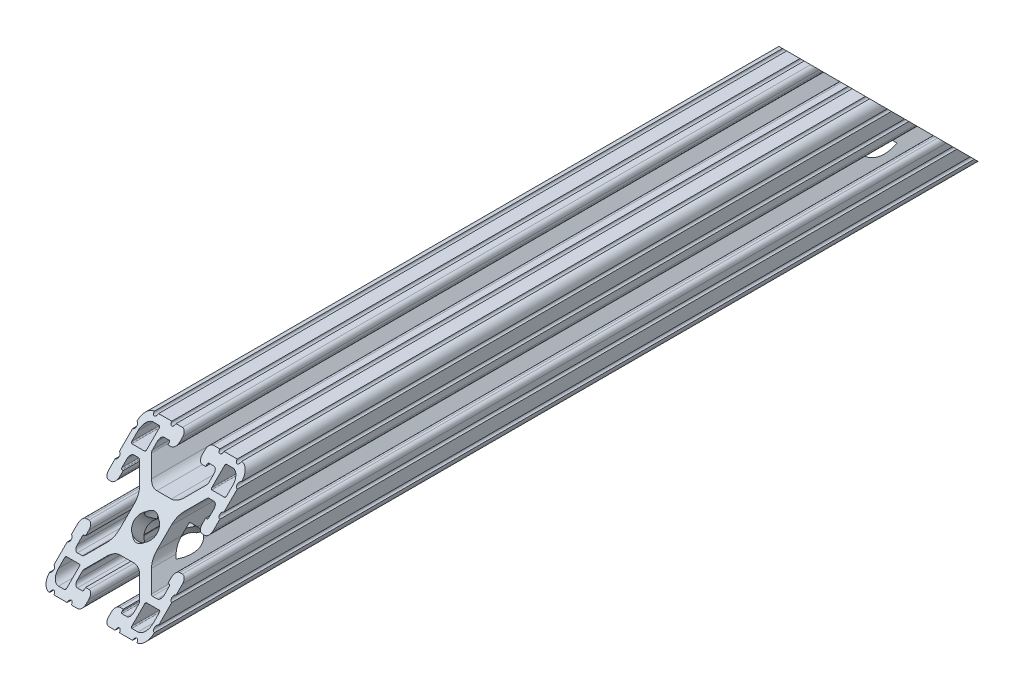
SolidWorks part; units mm, degrees
material "6105-T5 Aluminum"
ref_plane "Front Plane" through (0, 0, 0) normal (0, 0, 1) x (1, 0, 0)
ref_plane "Top Plane" through (0, 0, 0) normal (0, 1, 0) x (1, 0, 0)
ref_plane "Right Plane" through (0, 0, 0) normal (1, 0, 0) x (0, 0, -1)
sketch "Sketch1" plane through (0, 0, 0) normal (0, 0, 1) x (1, 0, 0)
  line L0 (16.8656, 11.8618) -> (12.2428, 11.8618)
  line L1 (11.8618, 12.2428) -> (11.8618, 16.8656)
  line L2 (12.2428, 17.2466) -> (14.4526, 17.2466)
  line L3 (17.2466, 14.4526) -> (17.2466, 12.2428)
  line L4 (-16.8656, -11.8618) -> (-12.2428, -11.8618)
  line L5 (-11.8618, -12.2428) -> (-11.8618, -16.8656)
  line L6 (-12.2428, -17.2466) -> (-14.4526, -17.2466)
  line L7 (-17.2466, -14.4526) -> (-17.2466, -12.2428)
  line L8 (11.8618, -16.8656) -> (11.8618, -12.2428)
  line L9 (12.2428, -11.8618) -> (16.8656, -11.8618)
  line L10 (17.2466, -12.2428) -> (17.2466, -14.4526)
  line L11 (14.4526, -17.2466) -> (12.2428, -17.2466)
  line L12 (-11.8618, 16.8656) -> (-11.8618, 12.2428)
  line L13 (-12.2428, 11.8618) -> (-16.8656, 11.8618)
  line L14 (-17.2466, 12.2428) -> (-17.2466, 14.4526)
  line L15 (-14.4526, 17.2466) -> (-12.2428, 17.2466)
  line L16 (-15.4432, -6.858) -> (-14.986, -6.858)
  line L17 (-14.986, -6.858) -> (-14.986, -5.6388)
  line L18 (-16.5608, -4.064) -> (-17.4752, -4.064)
  line L19 (-19.05, -5.6388) -> (-19.05, -7.9756)
  line L20 (-19.05, -9.4996) -> (-19.05, -14.3256)
  line L21 (-19.05, -15.8496) -> (-19.05, -15.875)
  line L22 (-15.875, -19.05) -> (-15.8496, -19.05)
  line L23 (-14.3256, -19.05) -> (-9.4996, -19.05)
  line L24 (-7.9756, -19.05) -> (-5.6388, -19.05)
  line L25 (-4.064, -17.4752) -> (-4.064, -16.5608)
  line L26 (-5.6388, -14.986) -> (-6.858, -14.986)
  line L27 (-6.858, -14.986) -> (-6.858, -15.4432)
  line L28 (-7.239, -15.8242) -> (-9.017, -15.8242)
  line L29 (-10.287, -14.5542) -> (-10.287, -12.8105)
  line L30 (-10.0266, -12.1819) -> (-5.9739, -8.1292)
  line L31 (-2.6153, -6.738) -> (2.6153, -6.738)
  line L32 (5.9739, -8.1292) -> (10.0266, -12.1819)
  line L33 (10.287, -12.8105) -> (10.287, -14.5542)
  line L34 (9.017, -15.8242) -> (7.239, -15.8242)
  line L35 (6.858, -15.4432) -> (6.858, -14.986)
  line L36 (6.858, -14.986) -> (5.6388, -14.986)
  line L37 (4.064, -16.5608) -> (4.064, -17.4752)
  line L38 (5.6388, -19.05) -> (7.9756, -19.05)
  line L39 (9.4996, -19.05) -> (14.3256, -19.05)
  line L40 (15.8496, -19.05) -> (15.875, -19.05)
  line L41 (19.05, -15.875) -> (19.05, -15.8496)
  line L42 (19.05, -14.3256) -> (19.05, -9.4996)
  line L43 (19.05, -7.9756) -> (19.05, -5.6388)
  line L44 (17.4752, -4.064) -> (16.5608, -4.064)
  line L45 (14.986, -5.6388) -> (14.986, -6.858)
  line L46 (14.986, -6.858) -> (15.4432, -6.858)
  line L47 (15.8242, -7.239) -> (15.8242, -9.017)
  line L48 (14.5542, -10.287) -> (12.8105, -10.287)
  line L49 (12.1819, -10.0266) -> (8.1292, -5.9739)
  line L50 (6.738, -2.6153) -> (6.738, 2.6153)
  line L51 (8.1292, 5.9739) -> (12.1819, 10.0266)
  line L52 (12.8105, 10.287) -> (14.5542, 10.287)
  line L53 (15.8242, 9.017) -> (15.8242, 7.239)
  line L54 (15.4432, 6.858) -> (14.986, 6.858)
  line L55 (14.986, 6.858) -> (14.986, 5.6388)
  line L56 (16.5608, 4.064) -> (17.4752, 4.064)
  line L57 (19.05, 5.6388) -> (19.05, 7.9756)
  line L58 (19.05, 9.4996) -> (19.05, 14.3256)
  line L59 (19.05, 15.8496) -> (19.05, 15.875)
  line L60 (15.875, 19.05) -> (15.8496, 19.05)
  line L61 (14.3256, 19.05) -> (9.4996, 19.05)
  line L62 (7.9756, 19.05) -> (5.6388, 19.05)
  line L63 (4.064, 17.4752) -> (4.064, 16.5608)
  line L64 (5.6388, 14.986) -> (6.858, 14.986)
  line L65 (6.858, 14.986) -> (6.858, 15.4432)
  line L66 (7.239, 15.8242) -> (9.017, 15.8242)
  line L67 (10.287, 14.5542) -> (10.287, 12.8105)
  line L68 (10.0266, 12.1819) -> (5.9739, 8.1292)
  line L69 (2.6153, 6.738) -> (-2.6153, 6.738)
  line L70 (-5.9739, 8.1292) -> (-10.0266, 12.1819)
  line L71 (-10.287, 12.8105) -> (-10.287, 14.5542)
  line L72 (-9.017, 15.8242) -> (-7.239, 15.8242)
  line L73 (-6.858, 15.4432) -> (-6.858, 14.986)
  line L74 (-6.858, 14.986) -> (-5.6388, 14.986)
  line L75 (-4.064, 16.5608) -> (-4.064, 17.4752)
  line L76 (-5.6388, 19.05) -> (-7.9756, 19.05)
  line L77 (-9.4996, 19.05) -> (-14.3256, 19.05)
  line L78 (-15.8496, 19.05) -> (-15.875, 19.05)
  line L79 (-19.05, 15.875) -> (-19.05, 15.8496)
  line L80 (-19.05, 14.3256) -> (-19.05, 9.4996)
  line L81 (-19.05, 7.9756) -> (-19.05, 5.6388)
  line L82 (-17.4752, 4.064) -> (-16.5608, 4.064)
  line L83 (-14.986, 5.6388) -> (-14.986, 6.858)
  line L84 (-14.986, 6.858) -> (-15.4432, 6.858)
  line L85 (-15.8242, 7.239) -> (-15.8242, 9.017)
  line L86 (-14.5542, 10.287) -> (-12.8105, 10.287)
  line L87 (-12.1819, 10.0266) -> (-8.1292, 5.9739)
  line L88 (-6.738, 2.6153) -> (-6.738, -2.6153)
  line L89 (-8.1292, -5.9739) -> (-12.1819, -10.0266)
  line L90 (-12.8105, -10.287) -> (-14.5542, -10.287)
  line L91 (-15.8242, -9.017) -> (-15.8242, -7.239)
  arc A0 (11.8618, 12.2428) -> (12.2428, 11.8618) centre (12.2428, 12.2428) ccw
  arc A1 (12.2428, 17.2466) -> (11.8618, 16.8656) centre (12.2428, 16.8656) ccw
  arc A2 (17.2466, 14.4526) -> (14.4526, 17.2466) centre (14.4526, 14.4526) ccw
  arc A3 (16.8656, 11.8618) -> (17.2466, 12.2428) centre (16.8656, 12.2428) ccw
  arc A4 (-11.8618, -12.2428) -> (-12.2428, -11.8618) centre (-12.2428, -12.2428) ccw
  arc A5 (-12.2428, -17.2466) -> (-11.8618, -16.8656) centre (-12.2428, -16.8656) ccw
  arc A6 (-17.2466, -14.4526) -> (-14.4526, -17.2466) centre (-14.4526, -14.4526) ccw
  arc A7 (-16.8656, -11.8618) -> (-17.2466, -12.2428) centre (-16.8656, -12.2428) ccw
  circle A8 centre (0, 0) radius 3.3274
  arc A9 (12.2428, -11.8618) -> (11.8618, -12.2428) centre (12.2428, -12.2428) ccw
  arc A10 (17.2466, -12.2428) -> (16.8656, -11.8618) centre (16.8656, -12.2428) ccw
  arc A11 (14.4526, -17.2466) -> (17.2466, -14.4526) centre (14.4526, -14.4526) ccw
  arc A12 (11.8618, -16.8656) -> (12.2428, -17.2466) centre (12.2428, -16.8656) ccw
  arc A13 (-12.2428, 11.8618) -> (-11.8618, 12.2428) centre (-12.2428, 12.2428) ccw
  arc A14 (-17.2466, 12.2428) -> (-16.8656, 11.8618) centre (-16.8656, 12.2428) ccw
  arc A15 (-14.4526, 17.2466) -> (-17.2466, 14.4526) centre (-14.4526, 14.4526) ccw
  arc A16 (-11.8618, 16.8656) -> (-12.2428, 17.2466) centre (-12.2428, 16.8656) ccw
  arc A17 (-15.4432, -6.858) -> (-15.8242, -7.239) centre (-15.4432, -7.239) ccw
  arc A18 (-14.986, -5.6388) -> (-16.5608, -4.064) centre (-16.5608, -5.6388) ccw
  arc A19 (-17.4752, -4.064) -> (-19.05, -5.6388) centre (-17.4752, -5.6388) ccw
  arc A20 (-19.05, -9.4996) -> (-19.05, -7.9756) centre (-19.05, -8.7376) ccw
  arc A21 (-19.05, -15.8496) -> (-19.05, -14.3256) centre (-19.05, -15.0876) ccw
  arc A22 (-19.05, -15.875) -> (-15.875, -19.05) centre (-15.875, -15.875) ccw
  arc A23 (-14.3256, -19.05) -> (-15.8496, -19.05) centre (-15.0876, -19.05) ccw
  arc A24 (-7.9756, -19.05) -> (-9.4996, -19.05) centre (-8.7376, -19.05) ccw
  arc A25 (-5.6388, -19.05) -> (-4.064, -17.4752) centre (-5.6388, -17.4752) ccw
  arc A26 (-4.064, -16.5608) -> (-5.6388, -14.986) centre (-5.6388, -16.5608) ccw
  arc A27 (-7.239, -15.8242) -> (-6.858, -15.4432) centre (-7.239, -15.4432) ccw
  arc A28 (-10.287, -14.5542) -> (-9.017, -15.8242) centre (-9.017, -14.5542) ccw
  arc A29 (-10.0266, -12.1819) -> (-10.287, -12.8105) centre (-9.398, -12.8105) ccw
  arc A30 (-2.6153, -6.738) -> (-5.9739, -8.1292) centre (-2.6153, -11.4878) ccw
  arc A31 (5.9739, -8.1292) -> (2.6153, -6.738) centre (2.6153, -11.4878) ccw
  arc A32 (10.287, -12.8105) -> (10.0266, -12.1819) centre (9.398, -12.8105) ccw
  arc A33 (9.017, -15.8242) -> (10.287, -14.5542) centre (9.017, -14.5542) ccw
  arc A34 (6.858, -15.4432) -> (7.239, -15.8242) centre (7.239, -15.4432) ccw
  arc A35 (5.6388, -14.986) -> (4.064, -16.5608) centre (5.6388, -16.5608) ccw
  arc A36 (4.064, -17.4752) -> (5.6388, -19.05) centre (5.6388, -17.4752) ccw
  arc A37 (9.4996, -19.05) -> (7.9756, -19.05) centre (8.7376, -19.05) ccw
  arc A38 (15.8496, -19.05) -> (14.3256, -19.05) centre (15.0876, -19.05) ccw
  arc A39 (15.875, -19.05) -> (19.05, -15.875) centre (15.875, -15.875) ccw
  arc A40 (19.05, -14.3256) -> (19.05, -15.8496) centre (19.05, -15.0876) ccw
  arc A41 (19.05, -7.9756) -> (19.05, -9.4996) centre (19.05, -8.7376) ccw
  arc A42 (19.05, -5.6388) -> (17.4752, -4.064) centre (17.4752, -5.6388) ccw
  arc A43 (16.5608, -4.064) -> (14.986, -5.6388) centre (16.5608, -5.6388) ccw
  arc A44 (15.8242, -7.239) -> (15.4432, -6.858) centre (15.4432, -7.239) ccw
  arc A45 (14.5542, -10.287) -> (15.8242, -9.017) centre (14.5542, -9.017) ccw
  arc A46 (12.1819, -10.0266) -> (12.8105, -10.287) centre (12.8105, -9.398) ccw
  arc A47 (6.738, -2.6153) -> (8.1292, -5.9739) centre (11.4878, -2.6153) ccw
  arc A48 (8.1292, 5.9739) -> (6.738, 2.6153) centre (11.4878, 2.6153) ccw
  arc A49 (12.8105, 10.287) -> (12.1819, 10.0266) centre (12.8105, 9.398) ccw
  arc A50 (15.8242, 9.017) -> (14.5542, 10.287) centre (14.5542, 9.017) ccw
  arc A51 (15.4432, 6.858) -> (15.8242, 7.239) centre (15.4432, 7.239) ccw
  arc A52 (14.986, 5.6388) -> (16.5608, 4.064) centre (16.5608, 5.6388) ccw
  arc A53 (17.4752, 4.064) -> (19.05, 5.6388) centre (17.4752, 5.6388) ccw
  arc A54 (19.05, 9.4996) -> (19.05, 7.9756) centre (19.05, 8.7376) ccw
  arc A55 (19.05, 15.8496) -> (19.05, 14.3256) centre (19.05, 15.0876) ccw
  arc A56 (19.05, 15.875) -> (15.875, 19.05) centre (15.875, 15.875) ccw
  arc A57 (14.3256, 19.05) -> (15.8496, 19.05) centre (15.0876, 19.05) ccw
  arc A58 (7.9756, 19.05) -> (9.4996, 19.05) centre (8.7376, 19.05) ccw
  arc A59 (5.6388, 19.05) -> (4.064, 17.4752) centre (5.6388, 17.4752) ccw
  arc A60 (4.064, 16.5608) -> (5.6388, 14.986) centre (5.6388, 16.5608) ccw
  arc A61 (7.239, 15.8242) -> (6.858, 15.4432) centre (7.239, 15.4432) ccw
  arc A62 (10.287, 14.5542) -> (9.017, 15.8242) centre (9.017, 14.5542) ccw
  arc A63 (10.0266, 12.1819) -> (10.287, 12.8105) centre (9.398, 12.8105) ccw
  arc A64 (2.6153, 6.738) -> (5.9739, 8.1292) centre (2.6153, 11.4878) ccw
  arc A65 (-5.9739, 8.1292) -> (-2.6153, 6.738) centre (-2.6153, 11.4878) ccw
  arc A66 (-10.287, 12.8105) -> (-10.0266, 12.1819) centre (-9.398, 12.8105) ccw
  arc A67 (-9.017, 15.8242) -> (-10.287, 14.5542) centre (-9.017, 14.5542) ccw
  arc A68 (-6.858, 15.4432) -> (-7.239, 15.8242) centre (-7.239, 15.4432) ccw
  arc A69 (-5.6388, 14.986) -> (-4.064, 16.5608) centre (-5.6388, 16.5608) ccw
  arc A70 (-4.064, 17.4752) -> (-5.6388, 19.05) centre (-5.6388, 17.4752) ccw
  arc A71 (-9.4996, 19.05) -> (-7.9756, 19.05) centre (-8.7376, 19.05) ccw
  arc A72 (-15.8496, 19.05) -> (-14.3256, 19.05) centre (-15.0876, 19.05) ccw
  arc A73 (-15.875, 19.05) -> (-19.05, 15.875) centre (-15.875, 15.875) ccw
  arc A74 (-19.05, 14.3256) -> (-19.05, 15.8496) centre (-19.05, 15.0876) ccw
  arc A75 (-19.05, 7.9756) -> (-19.05, 9.4996) centre (-19.05, 8.7376) ccw
  arc A76 (-19.05, 5.6388) -> (-17.4752, 4.064) centre (-17.4752, 5.6388) ccw
  arc A77 (-16.5608, 4.064) -> (-14.986, 5.6388) centre (-16.5608, 5.6388) ccw
  arc A78 (-15.8242, 7.239) -> (-15.4432, 6.858) centre (-15.4432, 7.239) ccw
  arc A79 (-14.5542, 10.287) -> (-15.8242, 9.017) centre (-14.5542, 9.017) ccw
  arc A80 (-12.1819, 10.0266) -> (-12.8105, 10.287) centre (-12.8105, 9.398) ccw
  arc A81 (-6.738, 2.6153) -> (-8.1292, 5.9739) centre (-11.4878, 2.6153) ccw
  arc A82 (-8.1292, -5.9739) -> (-6.738, -2.6153) centre (-11.4878, -2.6153) ccw
  arc A83 (-12.8105, -10.287) -> (-12.1819, -10.0266) centre (-12.8105, -9.398) ccw
  arc A84 (-15.8242, -9.017) -> (-14.5542, -10.287) centre (-14.5542, -9.017) ccw
extrude "Extrude1" add sketch "Sketch1" against normal blind 152.4
sketch "Sketch2" plane through (19.05, 0, 0) normal (1, 0, 0) x (0, 0, -1)
  line L0 (0, -19.05) -> (0, 27.8801)
  line L1 (0, 27.8801) -> (46.9301, 27.8801)
  line L2 (46.9301, 27.8801) -> (0, -19.05)
  dimension "D1" = 45
extrude "Cut-Extrude1" cut sketch "Sketch2" against normal through all
sketch "Sketch3" plane through (0, -9.525, -9.525) normal (0, 0.7071, 0.7071) x (1, 0, 0)
  circle A0 centre (0, 13.4704) radius 4.1656
  dimension "D1" = 8.3312
extrude "Cut-Extrude2" cut sketch "Sketch3" along normal blind 16.764 from offset 6.35 offset against normal yes
sketch "Sketch4" plane through (0, -9.525, -9.525) normal (0, 0.7071, 0.7071) x (1, 0, 0)
  circle A0 centre (0, 13.4704) radius 9.525
  dimension "D1" = 19.05
extrude "Cut-Extrude3" cut sketch "Sketch4" against normal blind 37.592 from offset 6.35 offset against normal yes
mirror "Mirror1" about plane through (-15.4432, -7.239, -152.4) normal (0, 0, 1) of "Cut-Extrude3", "Cut-Extrude2", "Cut-Extrude1", "Extrude1"
